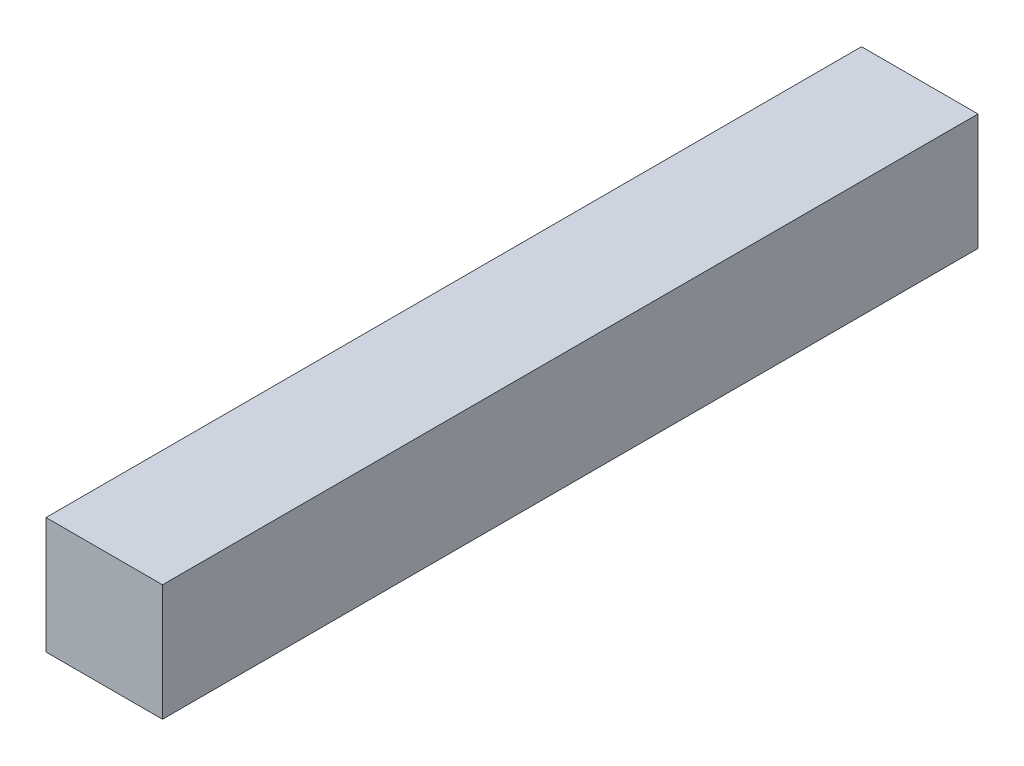
SolidWorks part; units mm, degrees
ref_plane "Front Plane" through (0, 0, 0) normal (0, 0, 1) x (1, 0, 0)
ref_plane "Top Plane" through (0, 0, 0) normal (0, 1, 0) x (1, 0, 0)
ref_plane "Right Plane" through (0, 0, 0) normal (1, 0, 0) x (0, 0, -1)
sketch "Sketch1" plane through (0, 0, 0) normal (0, 0, 1) x (1, 0, 0)
  line L1 (25, -25) -> (-25, -25)
  line L2 (25, -25) -> (25, 25)
  line L3 (25, 25) -> (-25, 25)
  line L4 (-25, -25) -> (-25, 25)
  line L5 (25, -25) -> (-25, 25) construction
  line L6 (25, 25) -> (-25, -25) construction
  point P0 (0, 0)
  dimension "D1" = 50
  dimension "D2" = 50
extrude "Boss-Extrude1" add sketch "Sketch1" along normal blind 350
